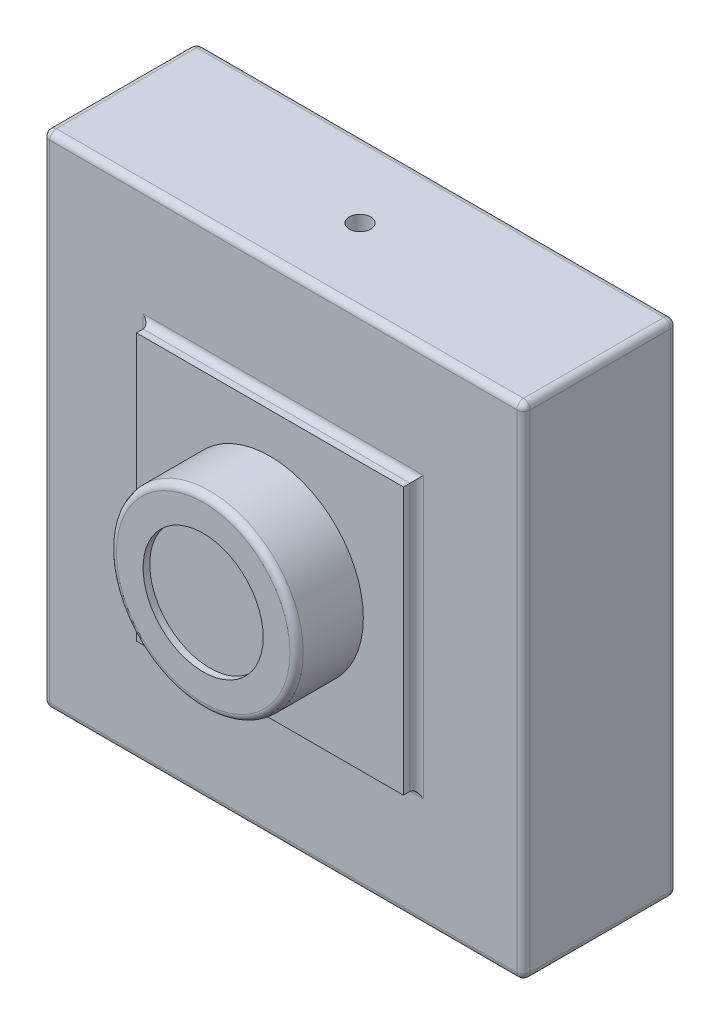
SolidWorks part; units mm, degrees
ref_plane "前视基准面" through (0, 0, 0) normal (0, 0, 1) x (1, 0, 0)
ref_plane "上视基准面" through (0, 0, 0) normal (0, 1, 0) x (1, 0, 0)
ref_plane "右视基准面" through (0, 0, 0) normal (1, 0, 0) x (0, 0, -1)
sketch "草图1" plane through (0, 0, 0) normal (0, 0, 1) x (1, 0, 0)
  line L1 (18, -18.75) -> (-18, -18.75)
  line L2 (18, -18.75) -> (18, 18.75)
  line L3 (18, 18.75) -> (-18, 18.75)
  line L4 (-18, -18.75) -> (-18, 18.75)
  line L5 (18, -18.75) -> (-18, 18.75) construction
  line L6 (18, 18.75) -> (-18, -18.75) construction
  point P0 (0, 0)
  dimension "D1" = 36
  dimension "D2" = 37.5
extrude "凸台-拉伸1" add sketch "草图1" along normal blind 11.5
sketch "草图2" plane through (0, 0, 11.5) normal (0, 0, 1) x (1, 0, 0)
  line L1 (10, -10) -> (-10, -10)
  line L2 (10, -10) -> (10, 10)
  line L3 (10, 10) -> (-10, 10)
  line L4 (-10, -10) -> (-10, 10)
  line L5 (10, -10) -> (-10, 10) construction
  line L6 (10, 10) -> (-10, -10) construction
  point P0 (0, 0)
  dimension "D1" = 20
  dimension "D2" = 20
extrude "凸台-拉伸2" add sketch "草图2" along normal blind 1
sketch "草图3" plane through (0, 0, 12.5) normal (0, 0, 1) x (1, 0, 0)
  circle A0 centre (0, 0) radius 7
  dimension "D1" = 14
extrude "凸台-拉伸3" add sketch "草图3" along normal blind 5
fillet "圆角1" radius 0.5 17 edges at (7, 0, 17.5) (0, -18.75, 0) (18, 0, 0) (0, 18.75, 0) (-18, 0, 0) (0, 18.75, 11.5) (18, 0, 11.5) (0, -18.75, 11.5) (-18, 0, 11.5) (0, -10, 11.5) (10, 0, 11.5) (0, 10, 11.5) (-10, 0, 11.5) (-18, 18.75, 5.75) (18, 18.75, 5.75) (18, -18.75, 5.75) (-18, -18.75, 5.75)
sketch "草图4" plane through (0, 0, 17.5) normal (0, 0, 1) x (1, 0, 0)
  circle A0 centre (0, 0) radius 4.5
  dimension "D1" = 9
extrude "切除-拉伸1" cut sketch "草图4" against normal blind 0.5
hole_wizard "M2 螺纹孔1" positions "草图5" profile "草图6" tap size "M2" standard "GB"
sketch "草图5" plane through (0, -18.75, 0) normal (0, -1, 0) x (-1, 0, 0)
  line L0 (-17.5, -5.75) -> (17.5, -5.75) construction
  line L1 (-17.5, -0.5) -> (-17.5, -11) construction
  line L2 (17.5, -11) -> (17.5, -0.5) construction
  point P0 (0, -5.75)
  point P10 (-1.2083, -2.6826)
sketch "草图6" plane through (0, -18.75, 5.75) normal (1, 0, 0) x (0, 0, -1)
  line L0 (0, 0) -> (0, 20.4807)
  line L1 (0, 20.4807) -> (0.8, 20)
  line L2 (0.8, 20) -> (0.8, 0)
  line L5 (0.8, 0) -> (0, 0)
  line L10 (0, 20.4807) -> (-0.8, 20) construction
  line L11 (0, -6.35) -> (0, 107.95) construction
  dimension "螺纹孔钻头直径" = 1.6
  dimension "螺纹孔钻头深度" = 20
  dimension "导头角度" = 118
cosmetic thread "孔螺蚊线1" parameters "D1"=4, "D2"=2
mirror "镜向1" about plane through (0, 0, 0) normal (0, 1, 0) of "M2 螺纹孔1"
